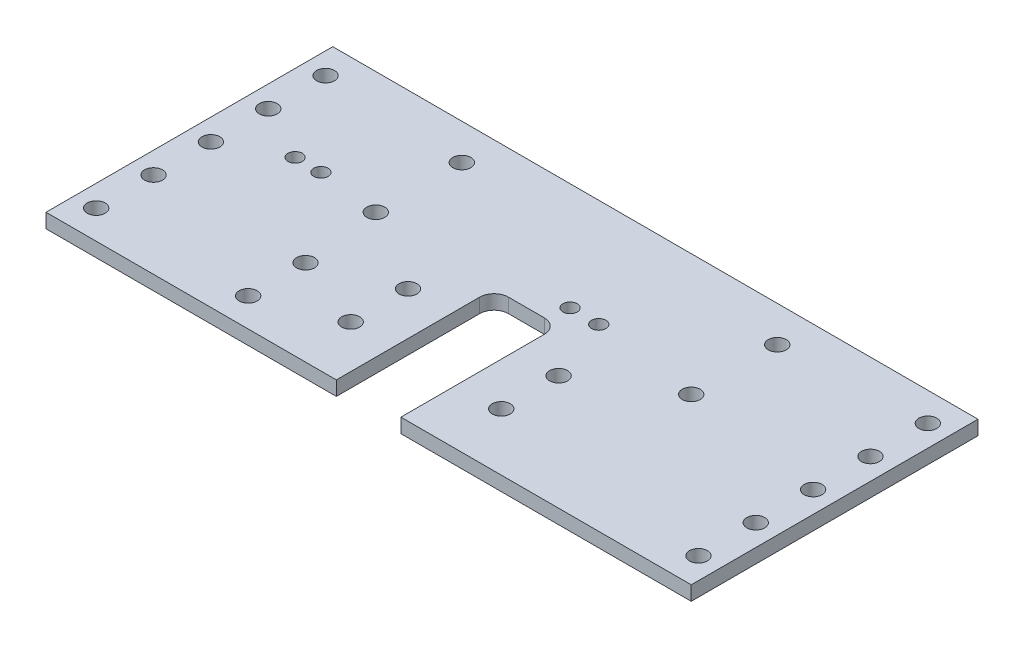
SolidWorks part; units mm, degrees
ref_plane "Front Plane" through (0, 0, 0) normal (0, 0, 1) x (1, 0, 0)
ref_plane "Top Plane" through (0, 0, 0) normal (0, 1, 0) x (1, 0, 0)
ref_plane "Right Plane" through (0, 0, 0) normal (1, 0, 0) x (0, 0, -1)
sketch "Sketch2" plane through (0, 0, 0) normal (0, 0, 1) x (1, 0, 0)
  line L3 (-503.1462, 54.6438) -> (-788.8962, 54.6438)
  line L5 (-503.1462, 54.6438) -> (-503.1462, 48.2938)
  line L7 (-503.1462, 48.2938) -> (-788.8962, 48.2938)
  line L8 (-788.8962, 54.6438) -> (-788.8962, 48.2938)
  dimension "D4" = 285.75
  dimension "D5" = 6.35
extrude "Stock" add sketch "Sketch2" against normal blind 127
sketch "Sketch3" plane through (0, 54.6438, 0) normal (0, 1, 0) x (1, 0, 0)
  line L0 (-503.1462, 0) -> (-788.8962, 0) construction
  line L1 (-631.7337, 31.75) -> (-660.3087, 31.75) construction
  line L2 (-734.2862, 31.75) -> (-763.4962, 31.75) construction
  line L3 (-503.1462, 127) -> (-503.1462, 0) construction
  line L4 (-503.1462, 0) -> (-788.8962, 0) construction
  line L5 (-646.0212, 0) -> (-646.0212, 127) construction
  line L6 (-503.1462, 127) -> (-788.8962, 127) construction
  line L7 (-638.0837, 69.85) -> (-653.9587, 69.85)
  line L9 (-788.8962, 127) -> (-788.8962, 0) construction
  line L16 (-631.7337, 0) -> (-660.3087, 0)
  line L17 (-631.7337, 0) -> (-631.7337, 63.5)
  line L18 (-503.1462, 127) -> (-503.1462, 0) construction
  line L19 (-631.7337, 63.5) -> (-660.3087, 63.5) construction
  line L20 (-503.1462, 127) -> (-788.8962, 127) construction
  line L21 (-788.8962, 127) -> (-788.8962, 0) construction
  line L22 (-503.1462, 0) -> (-788.8962, 0) construction
  line L23 (-503.1462, 127) -> (-503.1462, 0) construction
  line L24 (-660.3087, 0) -> (-660.3087, 63.5)
  line L25 (-734.2862, 0) -> (-763.4962, 0) construction
  line L26 (-734.2862, 0) -> (-734.2862, 63.5) construction
  line L27 (-734.2862, 63.5) -> (-763.4962, 63.5) construction
  line L28 (-763.4962, 0) -> (-763.4962, 63.5) construction
  arc A0 (-631.7337, 63.5) -> (-638.0837, 69.85) centre (-638.0837, 63.5) ccw
  arc A1 (-660.3087, 63.5) -> (-653.9587, 69.85) centre (-653.9587, 63.5) cw
  point P13 (-646.0212, 31.75)
  point P14 (-748.8912, 31.75)
  dimension "D8" = 6.35
  dimension "D1" = 40.005
  dimension "D2" = 28.575
  dimension "D3" = 63.5
  dimension "D4" = 63.5
  dimension "D5" = 142.875
  dimension "D7" = 29.21
extrude "Pedal Openings" cut sketch "Sketch3" against normal up to next (6.35 mm away) from surface at 0 starting at face at (-646.0212, 54.6438, -63.5)
sketch "Sketch5" plane through (0, 54.6438, 0) normal (0, 1, 0) x (1, 0, 0)
  line L0 (-612.6837, 0) -> (-612.6837, 66.675) construction
  line L1 (-646.0212, 66.675) -> (-612.6837, 66.675) construction
  line L2 (-503.1462, 0) -> (-503.1462, 127) construction
  line L3 (-612.6837, 66.675) -> (-587.2837, 66.675) construction
  line L4 (-646.0212, 0) -> (-646.0212, 66.675) construction
  line L5 (-679.3587, 0) -> (-679.3587, 66.675) construction
  line L6 (-631.7337, 0) -> (-587.2837, 0) construction
  line L7 (-503.1462, 0) -> (-631.7337, 0) construction
  line L8 (-587.2837, 66.675) -> (-587.2837, 0) construction
  line L9 (-646.0212, 66.675) -> (-679.3587, 66.675) construction
  line L10 (-660.3087, 0) -> (-788.8962, 0) construction
  line L11 (-631.7337, 0) -> (-446.1467, 0) construction
  line L12 (-631.7337, 0) -> (-631.7337, 69.85) construction
  line L13 (-631.7337, 69.85) -> (-446.1467, 69.85) construction
  line L15 (-679.3587, 0) -> (-734.6037, 0) construction
  line L16 (-734.6037, 0) -> (-734.6037, 63.5) construction
  line L17 (-734.6037, 63.5) -> (-437.376, 63.5) construction
  line L18 (-712.0612, 0) -> (-712.0612, 63.5) construction
  line L19 (-503.1462, 127) -> (-788.8962, 127) construction
  line L20 (-788.8962, 127) -> (-788.8962, 0) construction
  line L21 (-512.6712, 0) -> (-512.6712, 127) construction
  line L22 (-646.0212, 127) -> (-646.0212, -75.5796) construction
  line L23 (-512.6712, 127) -> (-779.3712, 127) construction
  line L24 (-779.3712, 0) -> (-779.3712, 127) construction
  line L25 (-595.2212, 127) -> (-595.2212, 63.5) construction
  line L26 (-715.8712, 63.5) -> (-715.8712, 127) construction
  line L27 (-595.2212, 63.5) -> (-563.4712, 63.5) construction
  line L28 (-563.4712, 63.5) -> (-563.4712, 127) construction
  line L29 (-576.1712, 63.5) -> (-576.1712, 127) construction
  line L30 (-728.5712, 63.5) -> (-728.5712, 127) construction
  line L31 (-696.8212, 63.5) -> (-728.5712, 63.5) construction
  line L32 (-696.8212, 127) -> (-696.8212, 63.5) construction
  line L34 (-754.7649, 50.8) -> (-754.7649, 127) construction
  line L35 (-734.2862, 50.8) -> (-754.7649, 50.8) construction
  line L36 (-631.7337, 69.85) -> (-636.1787, 69.85) construction
  line L37 (-636.1787, 69.85) -> (-636.1787, 79.375) construction
  line L38 (-636.1787, 79.375) -> (-623.4787, 79.375) construction
  circle A0 centre (-612.6837, 25.4) radius 3.9687
  circle A1 centre (-612.6837, 50.8) radius 3.9687
  circle A2 centre (-679.3587, 50.8) radius 3.9687
  circle A3 centre (-679.3587, 25.4) radius 3.9687
  circle A6 centre (-712.0612, 12.7) radius 3.9687
  circle A7 centre (-712.0612, 38.1) radius 3.9687
  circle A8 centre (-512.6712, 12.7) radius 3.9687
  circle A9 centre (-512.6712, 38.1) radius 3.9687
  circle A10 centre (-512.6712, 63.5) radius 3.9687
  circle A11 centre (-512.6712, 88.9) radius 3.9687
  circle A12 centre (-512.6712, 114.3) radius 3.9687
  circle A13 centre (-779.3712, 88.9) radius 3.9687
  circle A14 centre (-779.3712, 114.3) radius 3.9687
  circle A15 centre (-779.3712, 63.5) radius 3.9687
  circle A16 centre (-779.3712, 38.1) radius 3.9687
  circle A17 centre (-779.3712, 12.7) radius 3.9687
  circle A18 centre (-576.1712, 73.025) radius 3.9687
  circle A19 centre (-576.1712, 111.125) radius 3.9687
  circle A20 centre (-715.8712, 111.125) radius 3.9687
  circle A21 centre (-715.8712, 73.025) radius 3.9687
  circle A23 centre (-754.7649, 76.2) radius 3.175
  circle A24 centre (-743.3349, 76.2) radius 3.175
  circle A25 centre (-636.1787, 79.375) radius 3.175
  circle A26 centre (-623.4787, 79.375) radius 3.175
  point P60 (-646.0212, 127)
  dimension "D4" = 7.9375
  dimension "D5" = 7.9375
  dimension "D8" = 69.85
  dimension "D9" = 66.675
  dimension "D13" = 7.9375
  dimension "D14" = 7.9375
  dimension "D18" = 7.9375
  dimension "D20" = 7.9375
  dimension "D21" = 7.9375
  dimension "D22" = 7.9375
  dimension "D23" = 7.9375
  dimension "D36" = 7.9375
  dimension "D37" = 7.9375
  dimension "D39" = 6.35
  dimension "D40" = 6.35
  dimension "D47" = 6.35
  dimension "D48" = 6.35
  dimension "D2" = 15.875
  dimension "D3" = 25.4
  dimension "D6" = 54.2925
  dimension "D7" = 25.4
  dimension "D10" = 55.245
  dimension "D11" = 19.05
  dimension "D12" = 22.5425
  dimension "D15" = 12.7
  dimension "D16" = 25.4
  dimension "D17" = 9.525
  dimension "D19" = 12.7
  dimension "D24" = 25.4
  dimension "D25" = 25.4
  dimension "D26" = 25.4
  dimension "D27" = 25.4
  dimension "D28" = 50.8
  dimension "D29" = 47.625
  dimension "D30" = 63.5
  dimension "D32" = 31.75
  dimension "D33" = 19.05
  dimension "D34" = 9.525
  dimension "D38" = 34.1313
  dimension "D41" = 25.4
  dimension "D42" = 25.4
  dimension "D43" = 8.7312
  dimension "D44" = 4.445
  dimension "D45" = 9.525
  dimension "D46" = 12.7
extrude "Drilled Holes" cut sketch "Sketch5" against normal up to next
